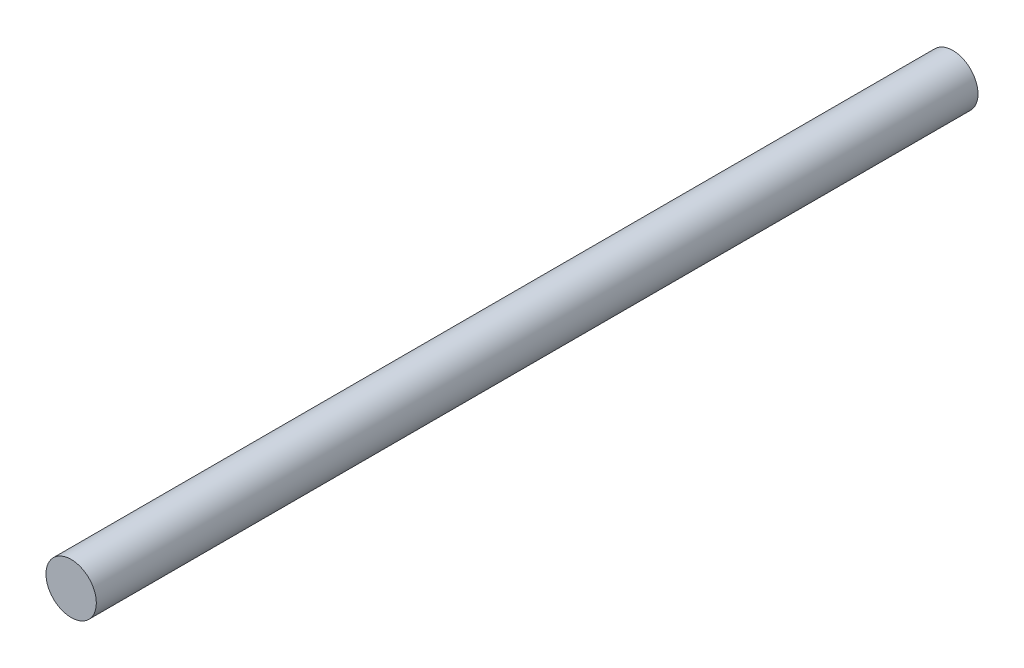
SolidWorks part; units mm, degrees
ref_plane "前视基准面" through (0, 0, 0) normal (0, 0, 1) x (1, 0, 0)
ref_plane "上视基准面" through (0, 0, 0) normal (0, 1, 0) x (1, 0, 0)
ref_plane "右视基准面" through (0, 0, 0) normal (1, 0, 0) x (0, 0, -1)
sketch "草图1" plane through (0, 0, 0) normal (0, 0, 1) x (1, 0, 0)
  circle A0 centre (0, 0) radius 2
  dimension "D1" = 4
extrude "凸台-拉伸1" add sketch "草图1" along normal blind 70
